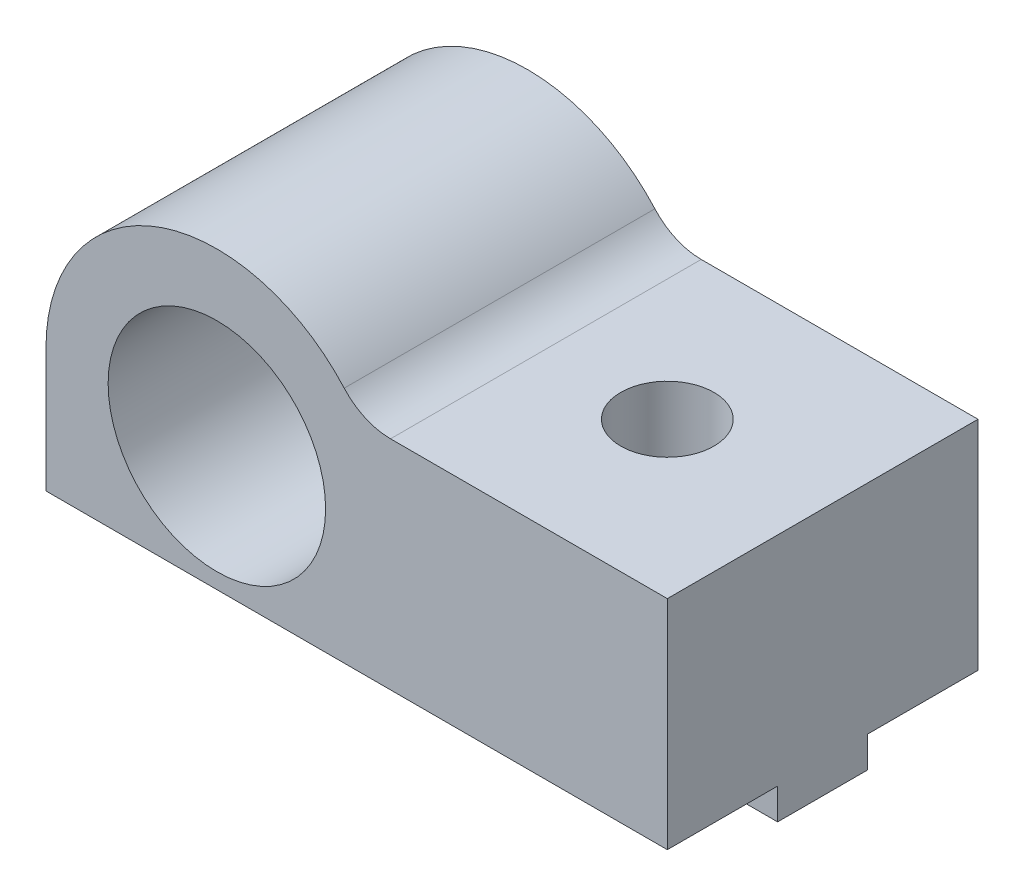
SolidWorks part; units mm, degrees
ref_plane "Front Plane" through (0, 0, 0) normal (0, 0, 1) x (1, 0, 0)
ref_plane "Top Plane" through (0, 0, 0) normal (0, 1, 0) x (1, 0, 0)
ref_plane "Right Plane" through (0, 0, 0) normal (1, 0, 0) x (0, 0, -1)
sketch "Sketch1" plane through (0, 0, 0) normal (0, 0, 1) x (1, 0, 0)
  line L0 (-5.5, 0) -> (-5.5, -4)
  line L1 (14.5, -4) -> (14.5, 3)
  line L3 (-5.5, -4) -> (14.5, -4)
  line L4 (14.5, 3) -> (4.6098, 3)
  arc A0 (-5.5, 0) -> (4.6098, 3) centre (0, 0) cw
  circle A1 centre (0, 0) radius 3.5
  dimension "D1" = 7
  dimension "D2" = 5.5
  dimension "D3" = 4
  dimension "D4" = 7
  dimension "D5" = 20
  dimension "D6" = 9.8902
extrude "Main" add sketch "Sketch1" along normal blind 10
sketch "Sketch3" plane through (0, -4, 0) normal (0, -1, 0) x (-1, 0, 0)
  line L0 (5.5, -10) -> (5.5, 0) construction
  line L1 (5.5, -6.45) -> (-14.5, -6.45)
  line L2 (5.5, -6.45) -> (5.5, -3.55)
  line L3 (5.5, -3.55) -> (-14.5, -3.55)
  line L4 (-14.5, -6.45) -> (-14.5, -3.55)
  line L5 (-14.5, -10) -> (-14.5, 0) construction
  line L6 (5.5, 0) -> (-14.5, 0) construction
  dimension "D1" = 2.9
  dimension "D2" = 3.55
extrude "MakerBeamRectangularGuide" add sketch "Sketch3" along normal blind 1
sketch "Sketch4" plane through (0, 3, 0) normal (0, 1, 0) x (1, 0, 0)
  line L0 (14.5, -10) -> (4.6098, -10) construction
  line L1 (14.5, -10) -> (14.5, 0) construction
  circle A0 centre (9.5, -5) radius 1.5
  dimension "D1" = 3
  dimension "D2" = 5
  dimension "D3" = 5
extrude "MakerBeamFixHole" cut sketch "Sketch4" against normal through all
fillet "Fillet1" radius 2 1 edges at (4.6098, 3, 5)
